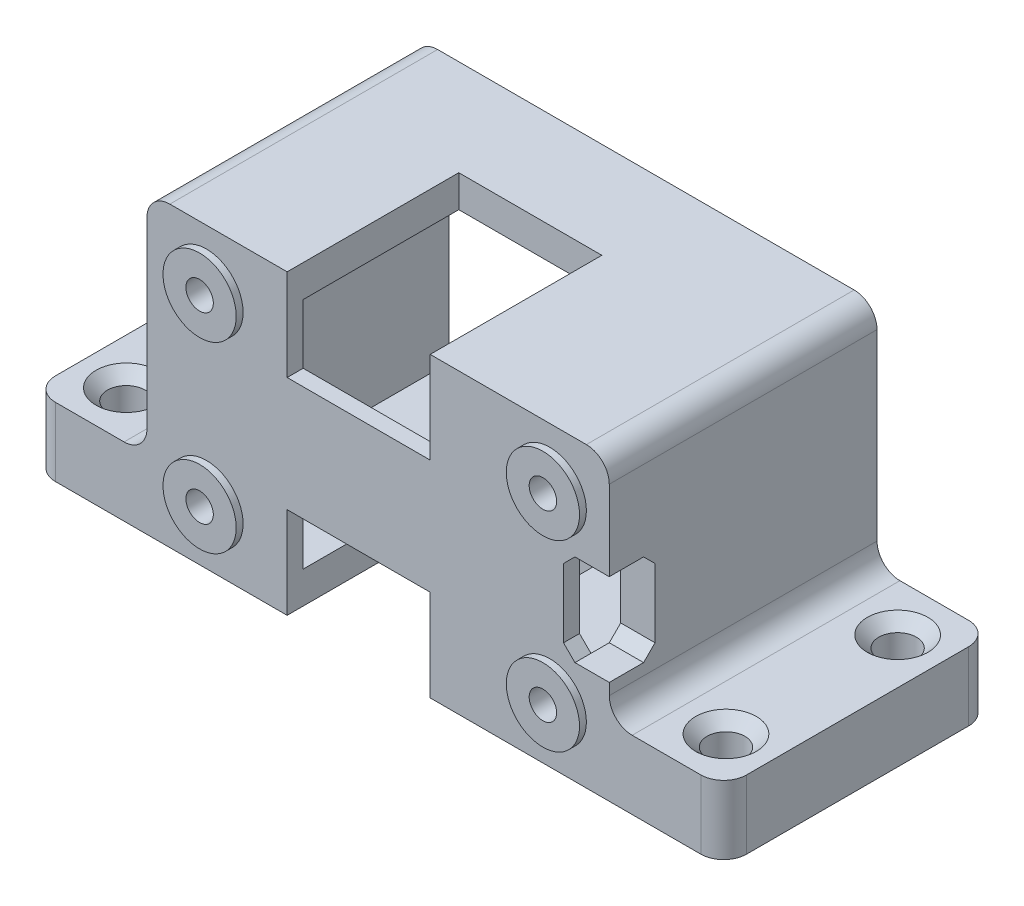
SolidWorks part; units mm, degrees
ref_plane "Front Plane" through (0, 0, 0) normal (0, 0, 1) x (1, 0, 0)
ref_plane "Top Plane" through (0, 0, 0) normal (0, 1, 0) x (1, 0, 0)
ref_plane "Right Plane" through (0, 0, 0) normal (1, 0, 0) x (0, 0, -1)
sketch "Sketch1" plane through (0, 0, 0) normal (0, 0, 1) x (1, 0, 0)
  line L1 (-17.2, 10.2) -> (17.2, 10.2)
  line L2 (-17.2, 10.2) -> (-17.2, -10.2)
  line L3 (-17.2, -10.2) -> (17.2, -10.2)
  line L4 (17.2, 10.2) -> (17.2, -10.2)
  line L5 (-17.2, 10.2) -> (17.2, -10.2) construction
  line L6 (-17.2, -10.2) -> (17.2, 10.2) construction
  line L7 (-20.2, 13) -> (20.2, 13)
  line L8 (-20.2, 13) -> (-20.2, -13)
  line L9 (-20.2, -13) -> (20.2, -13)
  line L10 (20.2, 13) -> (20.2, -13)
  line L11 (-20.2, 13) -> (20.2, -13) construction
  line L12 (-20.2, -13) -> (20.2, 13) construction
  point P0 (0, 0)
  point P6 (0, 0)
  dimension "D1" = 3
  dimension "D2" = 2.8
  dimension "D3" = 34.4
  dimension "D4" = 20.4
extrude "Boss-Extrude1" add sketch "Sketch1" along normal blind 22
sketch "Sketch2" plane through (0, 0, 22) normal (0, 0, 1) x (1, 0, 0)
  line L1 (-20.2, 13) -> (20.2, 13)
  line L2 (-20.2, 13) -> (-20.2, -13)
  line L3 (-20.2, -13) -> (20.2, -13)
  line L4 (20.2, 13) -> (20.2, -13)
extrude "Boss-Extrude2" add sketch "Sketch2" along normal blind 1.4
sketch "Sketch3" plane through (0, 0, 23.4) normal (0, 0, 1) x (1, 0, 0)
  line L0 (20.2, 13) -> (-20.2, 13) construction
  line L1 (-7.95, 13) -> (4.55, 13)
  line L2 (-7.95, 13) -> (-7.95, 5)
  line L3 (-7.95, 5) -> (4.55, 5)
  line L4 (4.55, 13) -> (4.55, 5)
  line L5 (-20.2, 13) -> (-20.2, -13) construction
  line L7 (0, 0) -> (-27.4318, 0) construction
  line L8 (4.55, -13) -> (4.55, -5)
  line L9 (-7.95, -5) -> (4.55, -5)
  line L10 (-7.95, -13) -> (-7.95, -5)
  line L11 (-7.95, -13) -> (4.55, -13)
  dimension "D1" = 12.25
  dimension "D2" = 12.5
  dimension "D3" = 8
extrude "Cut-Extrude1" cut sketch "Sketch3" against normal blind 15
sketch "Sketch4" plane through (0, 0, 23.4) normal (0, 0, 1) x (1, 0, 0)
  line L0 (0, 0) -> (-26.0248, 0) construction
  line L1 (0, 0) -> (0, 16.438) construction
  circle A0 centre (-15, 8) radius 1.2
  circle A1 centre (-15, -8) radius 1.2
  circle A2 centre (15, 8) radius 1.2
  circle A3 centre (15, -8) radius 1.2
  dimension "D1" = 8
  dimension "D2" = 15
  dimension "D3" = 2.4
extrude "Cut-Extrude2" cut sketch "Sketch4" against normal through all
sketch "Sketch5" plane through (0, 0, 0) normal (0, 0, -1) x (-1, 0, 0)
  line L1 (-20.2, -13) -> (-30.2, -13)
  line L2 (-20.2, -13) -> (-20.2, -7)
  line L3 (-20.2, -7) -> (-30.2, -7)
  line L4 (-30.2, -13) -> (-30.2, -7)
  line L5 (20.2, -13) -> (30.2, -13)
  line L6 (20.2, -13) -> (20.2, -7)
  line L7 (20.2, -7) -> (30.2, -7)
  line L8 (30.2, -13) -> (30.2, -7)
  dimension "D1" = 10
  dimension "D2" = 10
  dimension "D3" = 6
extrude "Boss-Extrude3" add sketch "Sketch5" against normal up to surface (23.4 mm away) up to face at (-16.2, -8, 23.4)
fillet "Fillet1" radius 2 8 edges at (20.2, 13, 11.7) (-20.2, 13, 11.7) (-30.2, -10, 23.4) (-30.2, -10, 0) (30.2, -10, 23.4) (30.2, -10, 0) (-20.2, -7, 11.7) (20.2, -7, 11.7)
sketch "Sketch6" plane through (0, -7, 0) normal (0, 1, 0) x (1, 0, 0)
  line L0 (0, 0) -> (0, -27.8771) construction
  line L1 (26.2, -19.2) -> (26.2, -4.2) construction
  line L2 (-18.2, -11.7) -> (36.8897, -11.7) construction
  line L3 (-18.2, 0) -> (-18.2, -23.4) construction
  line L5 (30.2, -21.4) -> (30.2, -2) construction
  circle A0 centre (26.2, -4.2) radius 1.65
  circle A1 centre (26.2, -19.2) radius 1.65
  circle A2 centre (-26.2, -19.2) radius 1.65
  circle A3 centre (-26.2, -4.2) radius 1.65
  dimension "D1" = 3.3
  dimension "D2" = 15
  dimension "D3" = 4
extrude "Cut-Extrude3" cut sketch "Sketch6" against normal through all
chamfer "Chamfer1" distance 1 angle 45 4 edges at (-24.55, -7, 4.2) (-24.55, -7, 19.2) (24.55, -7, 4.2) (24.55, -7, 19.2)
sketch "Sketch8" plane through (0, 0, 23.4) normal (0, 0, 1) x (1, 0, 0)
  line L0 (20.2, -5) -> (20.2, 11) construction
  line L1 (20.2, 4) -> (16.2, 4)
  line L2 (20.2, 4) -> (20.2, -4)
  line L3 (20.2, -4) -> (16.2, -4)
  line L4 (16.2, 4) -> (16.2, -4)
  line L5 (0, 0) -> (31.7408, 0) construction
  dimension "D1" = 8
  dimension "D2" = 4
extrude "Cut-Extrude4" cut sketch "Sketch8" against normal blind 4
chamfer "Chamfer2" distance 1 angle 45 4 edges at (16.2, -4, 22.7) (16.2, 4, 22.7) (18.7, 4, 19.4) (18.7, -4, 19.4)
sketch "Sketch9" plane through (0, 0, 23.4) normal (0, 0, 1) x (1, 0, 0)
  circle A0 centre (15, 8) radius 1.2 construction
  circle A1 centre (15, -8) radius 1.2 construction
  circle A2 centre (-15, -8) radius 1.2 construction
  circle A3 centre (-15, 8) radius 1.2 construction
  circle A4 centre (15, 8) radius 1.2
  circle A5 centre (15, -8) radius 1.2
  circle A6 centre (-15, -8) radius 1.2
  circle A7 centre (-15, 8) radius 1.2
  circle A8 centre (-15, 8) radius 3.2
  circle A9 centre (-15, -8) radius 3.2
  circle A10 centre (15, -8) radius 3.2
  circle A11 centre (15, 8) radius 3.2
  dimension "D1" = 2
extrude "Boss-Extrude4" add sketch "Sketch9" along normal blind 0.6
